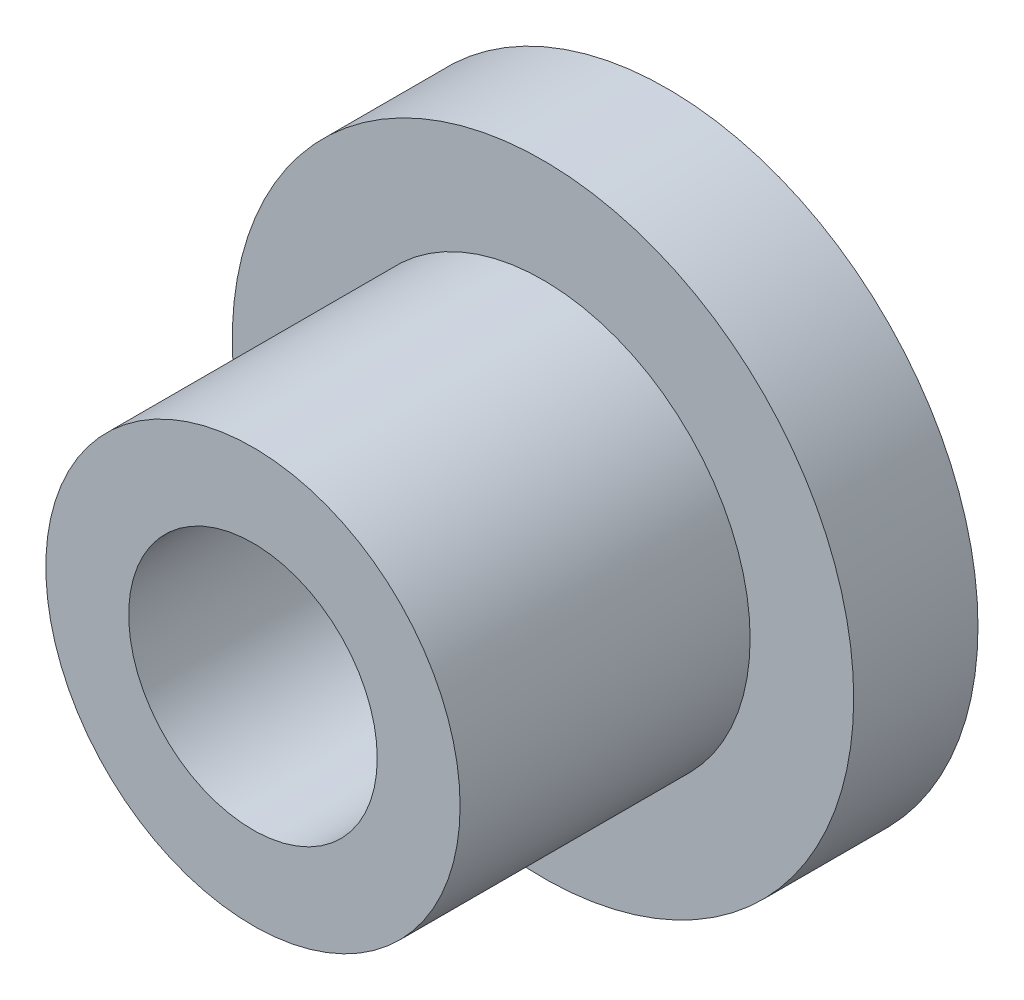
SolidWorks part; units mm, degrees
ref_plane "Ön Düzlem" through (0, 0, 0) normal (0, 0, 1) x (1, 0, 0)
ref_plane "Üst Düzlem" through (0, 0, 0) normal (0, 1, 0) x (1, 0, 0)
ref_plane "Sağ Düzlem" through (0, 0, 0) normal (1, 0, 0) x (0, 0, -1)
sketch "Çizim1" plane through (0, 0, 0) normal (0, 0, 1) x (1, 0, 0)
  circle A0 centre (0, 0) radius 15
  dimension "D1" = 30
extrude "Yükseklik-Ekstrüzyon1" add sketch "Çizim1" along normal blind 6
sketch "Çizim2" plane through (0, 0, 6) normal (0, 0, 1) x (1, 0, 0)
  circle A0 centre (0, 0) radius 10
  dimension "D1" = 20
extrude "Yükseklik-Ekstrüzyon2" add sketch "Çizim2" along normal blind 14
sketch "Çizim3" plane through (0, 0, 20) normal (0, 0, 1) x (1, 0, 0)
  circle A0 centre (0, 0) radius 6
  dimension "D1" = 12
extrude "Kes-Ekstrüzyon1" cut sketch "Çizim3" against normal through all
